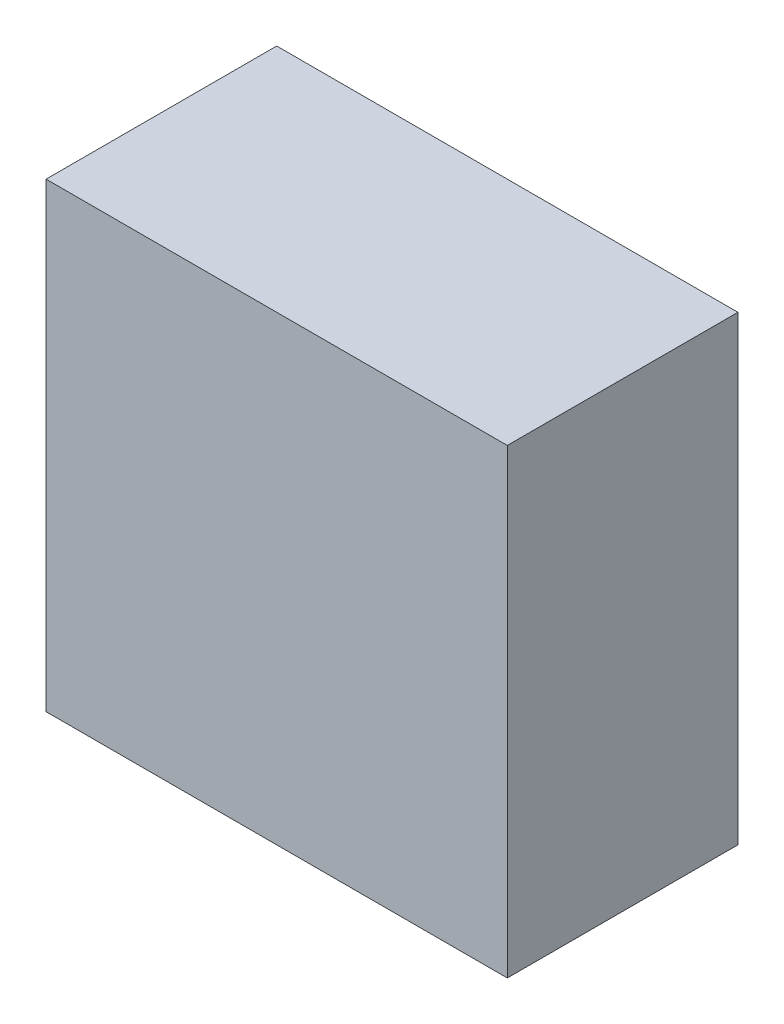
SolidWorks part; units mm, degrees
ref_plane "前视基准面" through (0, 0, 0) normal (0, 0, 1) x (1, 0, 0)
ref_plane "上视基准面" through (0, 0, 0) normal (0, 1, 0) x (1, 0, 0)
ref_plane "右视基准面" through (0, 0, 0) normal (1, 0, 0) x (0, 0, -1)
sketch "草图1" plane through (0, 0, 0) normal (0, 0, 1) x (1, 0, 0)
  line L1 (30, -30) -> (-30, -30)
  line L2 (30, -30) -> (30, 30)
  line L3 (30, 30) -> (-30, 30)
  line L4 (-30, -30) -> (-30, 30)
  line L5 (30, -30) -> (-30, 30) construction
  line L6 (30, 30) -> (-30, -30) construction
  point P0 (0, 0)
  dimension "D1" = 60
  dimension "D2" = 60
extrude "凸台-拉伸1" add sketch "草图1" along normal blind 30
